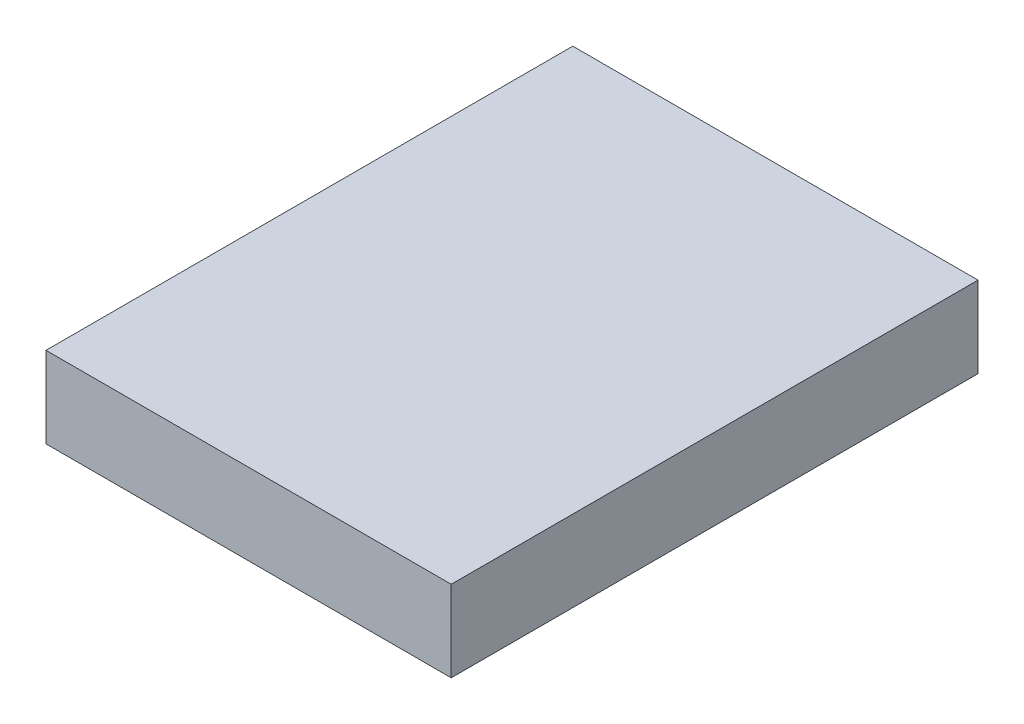
SolidWorks part; units mm, degrees
material "Pino"
ref_plane "Alzado" through (0, 0, 0) normal (0, 0, 1) x (1, 0, 0)
ref_plane "Planta" through (0, 0, 0) normal (0, 1, 0) x (1, 0, 0)
ref_plane "Vista lateral" through (0, 0, 0) normal (1, 0, 0) x (0, 0, -1)
sketch "Sketch1" plane through (0, 0, 0) normal (0, 1, 0) x (1, 0, 0)
  line L1 (-50, -65) -> (50, -65)
  line L2 (-50, -65) -> (-50, 65)
  line L3 (-50, 65) -> (50, 65)
  line L4 (50, -65) -> (50, 65)
  line L5 (-50, -65) -> (50, 65) construction
  line L6 (-50, 65) -> (50, -65) construction
  point P0 (0, 0)
  dimension "D1" = 100
  dimension "D2" = 130
extrude "Extrude1" add sketch "Sketch1" along normal blind 20
